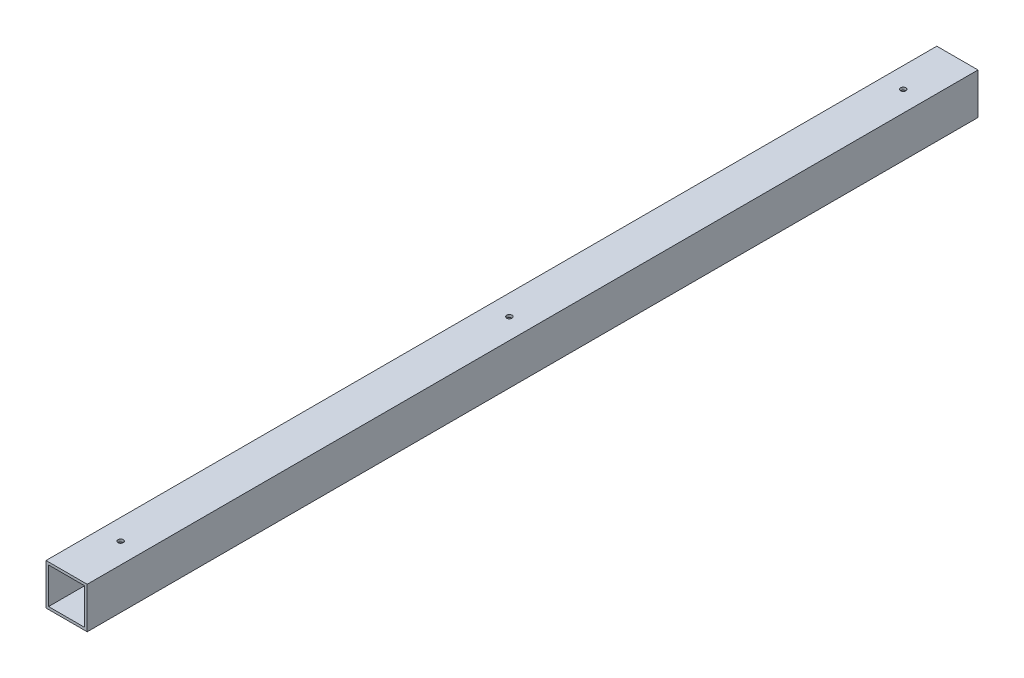
SolidWorks part; units mm, degrees
material "6061 Alloy"
ref_plane "Front Plane" through (0, 0, 0) normal (0, 0, 1) x (1, 0, 0)
ref_plane "Top Plane" through (0, 0, 0) normal (0, 1, 0) x (1, 0, 0)
ref_plane "Right Plane" through (0, 0, 0) normal (1, 0, 0) x (0, 0, -1)
sketch "Sketch1" plane through (0, 0, 0) normal (0, 0, 1) x (1, 0, 0)
  line L0 (2428.431, 50.8) -> (2428.431, 0) construction
  line L10 (2314.1312, 0) -> (2364.9312, 0)
  line L11 (2314.1312, 0) -> (2314.1312, 50.8)
  line L12 (2314.1312, 50.8) -> (2364.9312, 50.8)
  line L13 (2364.9312, 0) -> (2364.9312, 50.8)
  line L15 (2317.3062, 3.175) -> (2317.3062, 47.625)
  line L16 (2317.3062, 47.625) -> (2361.7562, 47.625)
  line L17 (2361.7562, 3.175) -> (2361.7562, 47.625)
  line L18 (2317.3062, 3.175) -> (2361.7562, 3.175)
  dimension "D1" = 3.175
  dimension "D2" = 50.8
  dimension "D3" = 50.8
  dimension "D4" = 63.4998
extrude "Boss-Extrude1" add sketch "Sketch1" along normal blind 1098.55
sketch "Sketch2" plane through (0, 50.8, 0) normal (0, 1, 0) x (1, 0, 0)
  line L0 (2364.9312, -1098.55) -> (2314.1312, -1098.55) construction
  line L2 (2314.1312, -549.275) -> (2364.9312, -549.275) construction
  line L3 (2314.1312, -1098.55) -> (2314.1312, 0) construction
  line L4 (2364.9312, -1098.55) -> (2364.9312, 0) construction
  line L5 (2364.9312, 0) -> (2314.1312, 0) construction
  circle A0 centre (2339.5312, -552.45) radius 3.302
  circle A1 centre (2339.5312, -1031.875) radius 3.302
  circle A2 centre (2339.5312, -66.802) radius 3.302
  dimension "D1" = 6.604
  dimension "D2" = 485.648
  dimension "D4" = 66.802
  dimension "D3" = 25.4
  dimension "D5" = 25.4
  dimension "D6" = 66.675
  dimension "D7" = 479.425
extrude "Cut-Extrude1" cut sketch "Sketch2" against normal blind 50.8
